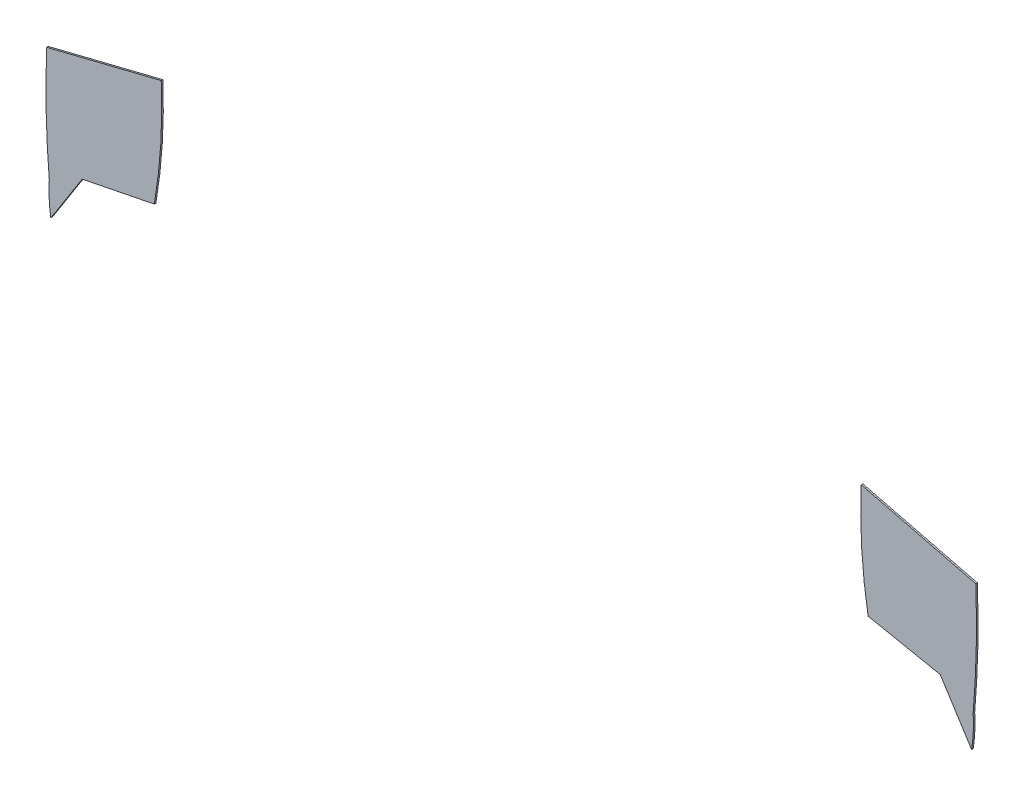
SolidWorks part; units mm, degrees
ref_plane "Alzado" through (0, 0, 0) normal (0, 0, 1) x (1, 0, 0)
ref_plane "Planta" through (0, 0, 0) normal (0, 1, 0) x (1, 0, 0)
ref_plane "Vista lateral" through (0, 0, 0) normal (1, 0, 0) x (0, 0, -1)
sketch "Model" plane through (0, 0, 0) normal (0, 0, 1) x (1, 0, 0)
  line L0 (12.4705, -1.3452) -> (5.1283, -3.1675)
  line L1 (57.3443, -1.346) -> (64.6847, -3.1685)
  line L2 (7.407, -9.3479) -> (12.028, -8.4238)
  line L3 (5.3932, -12.5111) -> (7.407, -9.3479)
  line L4 (64.4195, -12.512) -> (62.4058, -9.3488)
  line L5 (62.4058, -9.3488) -> (57.7848, -8.4246)
  arc A0 (5.1283, -3.1675) -> (5.2939, -10.443) centre (63.0463, -5.4892) ccw
  arc A1 (5.2939, -10.443) -> (5.3932, -12.5111) centre (14.21, -11.051) ccw
  arc A2 (57.3443, -1.346) -> (57.7848, -8.4246) centre (90.4391, -2.8392) ccw
  arc A3 (64.4195, -12.512) -> (64.5174, -10.4222) centre (55.5715, -11.0502) ccw
  arc A4 (64.5174, -10.4222) -> (64.681, -7.8541) centre (6.937, -5.4652) ccw
  arc A5 (64.681, -7.8541) -> (64.6847, -3.1685) centre (6.937, -5.4652) ccw
  arc A6 (12.028, -8.4238) -> (12.4705, -1.3452) centre (-20.4209, -2.8421) ccw
extrude "Saliente-Extruir1" add sketch "Model" along normal blind 0.1
